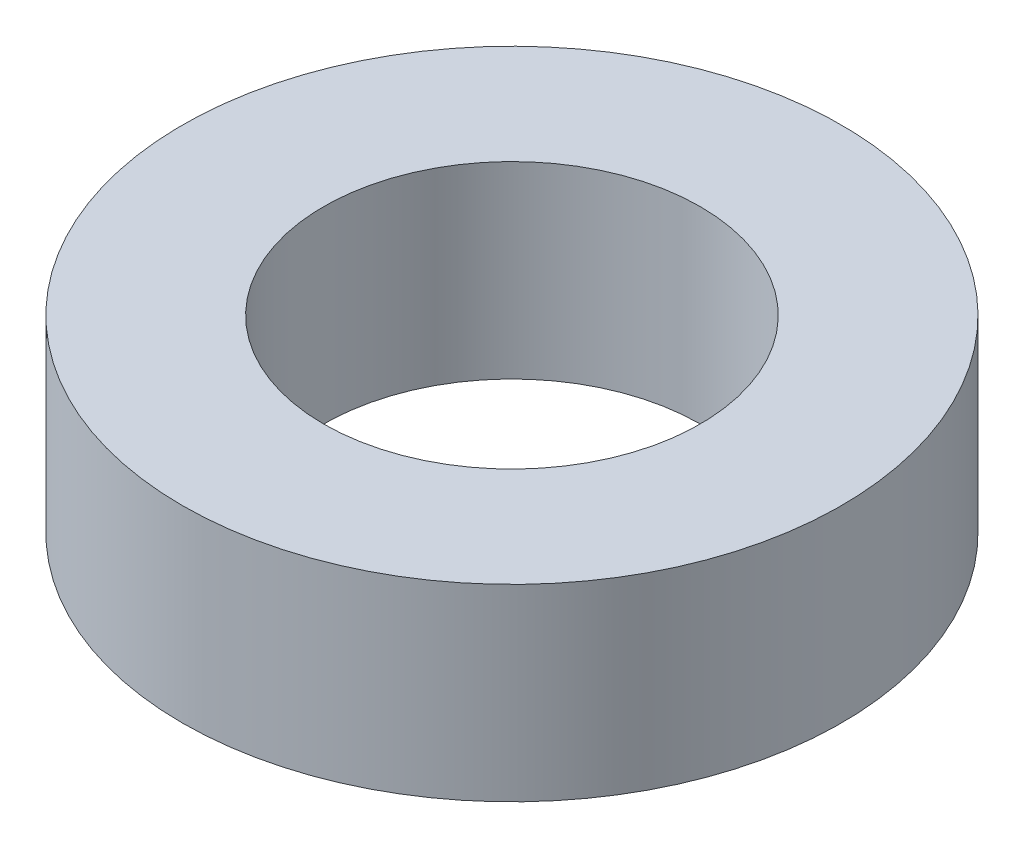
SolidWorks part; units mm, degrees
ref_plane "Front Plane" through (0, 0, 0) normal (0, 0, 1) x (1, 0, 0)
ref_plane "Top Plane" through (0, 0, 0) normal (0, 1, 0) x (1, 0, 0)
ref_plane "Right Plane" through (0, 0, 0) normal (1, 0, 0) x (0, 0, -1)
sketch "스케치1" plane through (0, 0, 0) normal (0, 1, 0) x (1, 0, 0)
  circle A0 centre (0, 0) radius 3.5
  circle A1 centre (0, 0) radius 2
extrude "보스-돌출1" add sketch "스케치1" along normal blind 2
